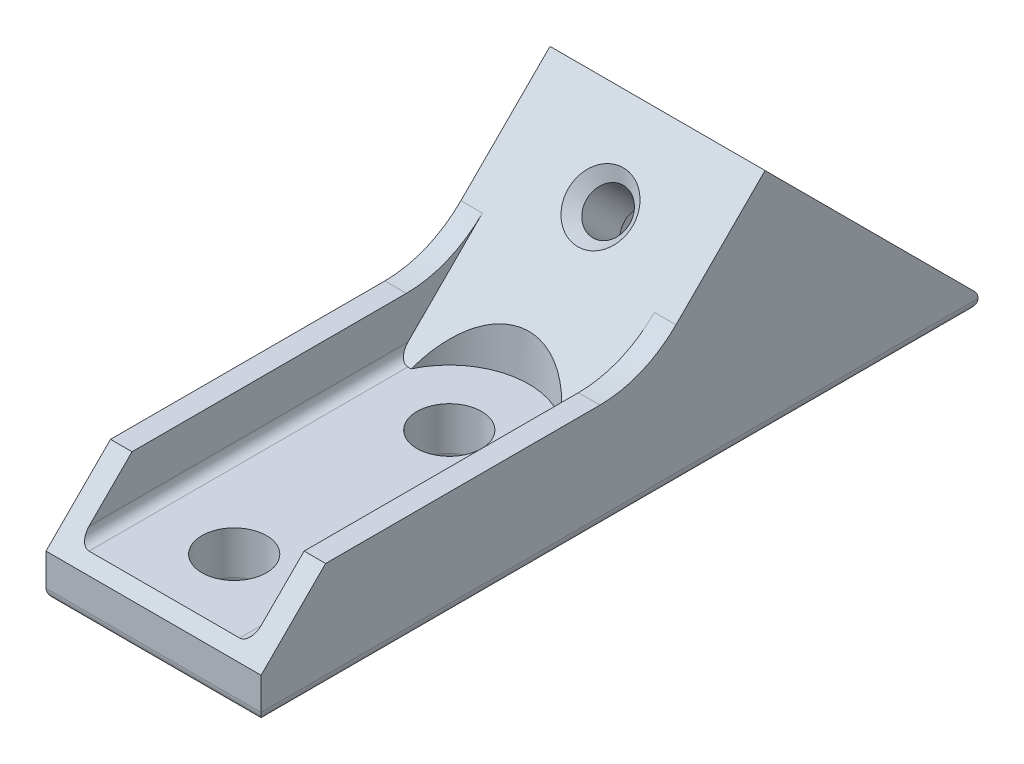
SolidWorks part; units mm, degrees
ref_plane "Front" through (0, 0, 0) normal (0, 0, 1) x (1, 0, 0)
ref_plane "Top" through (0, 0, 0) normal (0, 1, 0) x (1, 0, 0)
ref_plane "Right" through (0, 0, 0) normal (1, 0, 0) x (0, 0, -1)
other "Configuration Table"
sketch "Sketch1" plane through (0, 0, 0) normal (0, 1, 0) x (1, 0, 0)
  line L1 (-10, 20) -> (10, 20)
  line L2 (-10, 20) -> (-10, -20)
  line L3 (-10, -20) -> (10, -20)
  line L4 (10, 20) -> (10, -20)
  line L5 (-10, 20) -> (10, -20) construction
  line L6 (-10, -20) -> (10, 20) construction
  point P0 (0, 0)
  dimension "D1" = 20
  dimension "D2" = 40
extrude "Boss-Extrude1" add sketch "Sketch1" along normal blind 5
sketch "Sketch2" plane through (-10, 0, 0) normal (-1, 0, 0) x (0, 0, 1)
  line L0 (-5.6509, 0) -> (-26.8641, 21.2132)
  line L1 (-20, 0) -> (20, 0) construction
  line L2 (-26.8641, 21.2132) -> (-48.0773, 0)
  line L3 (-48.0773, 0) -> (-5.6509, 0)
  dimension "D1" = 30
  dimension "D2" = 30
extrude "Boss-Extrude2" add sketch "Sketch2" against normal blind 20
sketch "Sketch3" plane through (0, 5, 0) normal (0, 1, 0) x (1, 0, 0)
  line L0 (-10, -20) -> (10, -20) construction
  line L1 (-10, 10.6509) -> (-10, -20) construction
  circle A0 centre (0, -12.5) radius 3
  dimension "D1" = 7.5
  dimension "D2" = 10
extrude "Cut-Extrude1" cut sketch "Sketch3" against normal blind 15
pattern_linear "LPattern1" count 2 spacing 20 along (0, 0, -1) of "Cut-Extrude1"
sketch "Sketch4" plane through (0, 5, 0) normal (0, 1, 0) x (1, 0, 0)
  circle A0 centre (0, 7.5) radius 7.4
extrude "Cut-Extrude2" cut sketch "Sketch4" along normal blind 15
sketch "Sketch5" plane through (0, -2.8254, -2.8254) normal (0, 0.7071, 0.7071) x (1, 0, 0)
  line L0 (10, 33.9958) -> (-10, 33.9958) construction
  line L1 (10, 11.0668) -> (10, 33.9958) construction
  circle A0 centre (0, 26.4958) radius 2
  dimension "D1" = 7.5
  dimension "D2" = 10
extrude "Cut-Extrude3" cut sketch "Sketch5" against normal blind 50
sketch "Sketch6" plane through (0, -2.8254, -2.8254) normal (0, 0.7071, 0.7071) x (1, 0, 0)
  line L0 (-10, 11.0668) -> (-10, 33.9958) construction
  line L1 (0, 30.2486) -> (-3.25, 28.3722)
  line L2 (-3.25, 28.3722) -> (-3.25, 24.6194)
  line L3 (-3.25, 24.6194) -> (0, 22.743)
  line L4 (0, 22.743) -> (3.25, 24.6194)
  line L5 (3.25, 24.6194) -> (3.25, 28.3722)
  line L6 (3.25, 28.3722) -> (0, 30.2486)
  circle A0 centre (0, 26.4958) radius 3.25 construction
  dimension "D1" = 6.5
extrude "Cut-Extrude4" cut sketch "Sketch6" against normal blind 40 from offset 6 offset against normal yes
chamfer "Chamfer1" distance 1 angle 45 1 edges at (0, 14.4957, -20.1466)
fillet "Fillet2" radius 1 12 edges at (10, 0, -14.0386) (0, 0, -48.0773) (-10, 0, -14.0386) (0, 0, 20) (0, 0, 15.5) (0, 0, -4.5) (1.625, 0, -33.4903) (-1.625, 0, -33.4903) (-3.25, 0, -37.4707) (-1.625, 0, -41.4511) (1.625, 0, -41.4511) (3.25, 0, -37.4707)
sketch "Sketch7" plane through (0, 5, 0) normal (0, 1, 0) x (1, 0, 0)
  line L0 (-10, 10.6509) -> (-10, -20) construction
  line L1 (-10, -20) -> (-8, -20)
  line L2 (-10, -20) -> (-10, 25.9409)
  line L3 (-10, 25.9409) -> (-8, 25.9409)
  line L4 (-8, -20) -> (-8, 25.9409)
  dimension "D1" = 2
extrude "Boss-Extrude3" add sketch "Sketch7" along normal blind 5
pattern_linear "LPattern2" count 2 spacing 18 along (1, 0, 0) of "Boss-Extrude3"
fillet "Fillet3" radius 1 2 edges at (8, 5, 4.6746) (-8, 5, 4.6746)
chamfer "Chamfer2" distance 6 angle 45 1 edges at (9, 10, 20)
fillet "Fillet4" radius 10 2 edges at (-9, 10, -15.6509) (9, 10, -15.6509)
